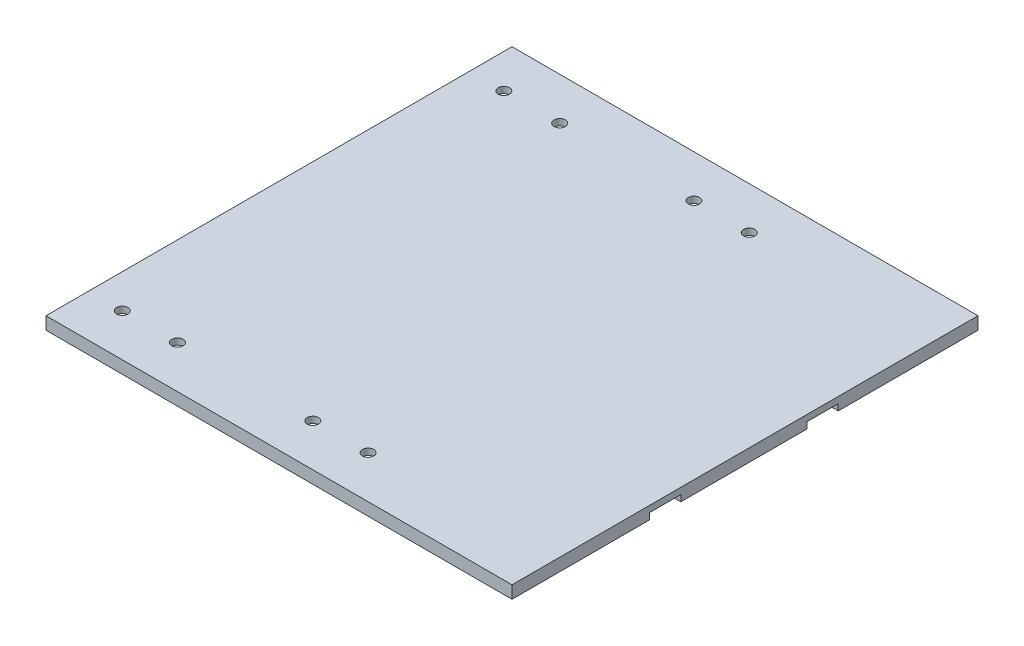
SolidWorks part; units mm, degrees
ref_plane "Plan de face" through (0, 0, 0) normal (0, 0, 1) x (1, 0, 0)
ref_plane "Plan de dessus" through (0, 0, 0) normal (0, 1, 0) x (1, 0, 0)
ref_plane "Plan de droite" through (0, 0, 0) normal (1, 0, 0) x (0, 0, -1)
sketch "Esquisse1" plane through (0, 0, 0) normal (0, 1, 0) x (1, 0, 0)
  line L1 (-74, 74) -> (74, 74)
  line L2 (-74, 74) -> (-74, -74)
  line L3 (-74, -74) -> (74, -74)
  line L4 (74, 74) -> (74, -74)
  line L5 (-74, 74) -> (74, -74) construction
  line L6 (-74, -74) -> (74, 74) construction
  point P0 (0, 0)
extrude "Boss.-Extru.1" add sketch "Esquisse1" along normal blind 4
sketch "Esquisse4" plane through (0, 0, 0) normal (0, 1, 0) x (1, 0, 0)
  line L0 (-72, -60.525) -> (-54.5, -60.525) construction
  line L5 (-54.5, -60.525) -> (-37, -60.525) construction
  circle A0 centre (-63.25, -60.525) radius 1.8
  circle A1 centre (-45.75, -60.525) radius 1.8
extrude "Enlèv. mat.-Extru.2" cut sketch "Esquisse4" along normal blind 4
sketch "Esquisse5" plane through (0, 0, 0) normal (0, 1, 0) x (1, 0, 0)
  line L1 (-72, -72) -> (-36.5, -72)
  line L2 (-72, -72) -> (-72, -48.5)
  line L3 (-72, -48.5) -> (-36.5, -48.5)
  line L4 (-36.5, -72) -> (-36.5, -48.5)
extrude "Enlèv. mat.-Extru.3" cut sketch "Esquisse5" along normal blind 2
sketch "Esquisse6" plane through (0, 0, 0) normal (0, 1, 0) x (1, 0, 0)
  line L0 (-72, -72) -> (-36.5, -72) construction
  line L1 (-36.5, -72) -> (-36.5, -48.5) construction
  line L2 (-36.5, -72) -> (-11.5, -72) construction
  line L3 (-11.5, -72) -> (23.6, -72) construction
  line L4 (-11.5, -72) -> (-11.5, -49.05) construction
  line L5 (-11.5, -49.05) -> (23.6, -49.05) construction
  line L6 (23.6, -49.05) -> (23.6, -72) construction
  line L7 (-11.5, -60.525) -> (6.05, -60.525) construction
  line L8 (6.05, -60.525) -> (23.6, -60.525) construction
  line L10 (-11.5, -72) -> (24, -72)
  line L11 (-11.5, -72) -> (-11.5, -48.5)
  line L12 (-11.5, -48.5) -> (24, -48.5)
  line L13 (24, -72) -> (24, -48.5)
  circle A0 centre (-2.725, -60.525) radius 1.8
  circle A1 centre (14.825, -60.525) radius 1.8
sketch "Esquisse8" plane through (0, 0, 0) normal (0, 1, 0) x (1, 0, 0)
  circle A0 centre (-2.725, -60.525) radius 1.8
  circle A1 centre (14.825, -60.525) radius 1.8
extrude "Enlèv. mat.-Extru.6" cut sketch "Esquisse8" along normal blind 4
sketch "Esquisse9" plane through (0, 0, 0) normal (0, 1, 0) x (1, 0, 0)
  line L1 (-11.5, -72) -> (24, -72)
  line L2 (-11.5, -72) -> (-11.5, -48.5)
  line L3 (-11.5, -48.5) -> (24, -48.5)
  line L4 (24, -72) -> (24, -48.5)
extrude "Enlèv. mat.-Extru.7" cut sketch "Esquisse9" along normal blind 2
sketch "Esquisse10" plane through (0, 0, 0) normal (0, 1, 0) x (1, 0, 0)
  line L0 (-72, 72) -> (69.8434, 72) construction
  line L1 (-11.5, -49.05) -> (-11.5, 72) construction
  line L2 (-36.5, -48.5) -> (-36.5, 72) construction
  line L3 (23.6, -49.05) -> (23.6, 72) construction
  line L4 (-72, -72) -> (-72, 72) construction
  line L5 (-11.5, 60.525) -> (6.05, 60.525) construction
  line L10 (6.05, 60.525) -> (23.6, 60.525) construction
  line L11 (-72, 60.525) -> (-54.25, 60.525) construction
  line L16 (-54.25, 60.525) -> (-36.5, 60.525) construction
  circle A0 centre (-2.725, 60.525) radius 1.8
  circle A1 centre (14.825, 60.525) radius 1.8
  circle A2 centre (-63.125, 60.525) radius 1.8
  circle A3 centre (-45.375, 60.525) radius 1.8
extrude "Enlèv. mat.-Extru.8" cut sketch "Esquisse10" along normal blind 4
sketch "Esquisse11" plane through (0, 0, 0) normal (0, 1, 0) x (1, 0, 0)
  line L0 (-72, -72) -> (-72, 72) construction
  line L1 (-36.5, -48.5) -> (-36.5, 72) construction
  line L2 (-11.5, -49.05) -> (-11.5, 72) construction
  line L3 (24, -48.5) -> (24, 72) construction
  line L9 (-72, 72) -> (-36.5, 72)
  line L10 (-72, 72) -> (-72, 48.5)
  line L11 (-72, 48.5) -> (-36.5, 48.5)
  line L12 (-36.5, 72) -> (-36.5, 48.5)
  line L13 (-11.5, 48.4877) -> (24, 48.4877)
  line L14 (-11.5, 48.4877) -> (-11.5, 72)
  line L15 (-11.5, 72) -> (24, 72)
  line L16 (24, 48.4877) -> (24, 72)
extrude "Enlèv. mat.-Extru.9" cut sketch "Esquisse11" along normal blind 2
sketch "Esquisse12" plane through (0, 0, 0) normal (0, 1, 0) x (1, 0, 0)
  line L0 (80.5612, -25.3842) -> (80.5612, -20.3842) construction
  line L1 (74.0521, 24.6158) -> (74.0521, 29.6158) construction
  line L2 (80.5612, -25.3842) -> (56.9202, -25.3842) construction
  line L3 (80.5612, -25.3842) -> (80.5612, -30.3842) construction
  line L4 (74.0521, 24.6158) -> (56.9202, 24.6158) construction
  line L5 (80.5612, -20.3842) -> (56.9202, -20.3842)
  line L6 (80.5612, -20.3842) -> (80.5612, -30.3842)
  line L7 (80.5612, -30.3842) -> (56.9202, -30.3842)
  line L8 (56.9202, -20.3842) -> (56.9202, -30.3842)
  line L9 (74.0521, 24.6158) -> (74.0521, 19.6158) construction
  line L11 (74.0521, 29.6158) -> (56.9202, 29.6158)
  line L12 (74.0521, 29.6158) -> (74.0521, 19.6158)
  line L13 (74.0521, 19.6158) -> (56.9202, 19.6158)
  line L14 (56.9202, 29.6158) -> (56.9202, 19.6158)
extrude "Enlèv. mat.-Extru.12" cut sketch "Esquisse12" along normal blind 2
